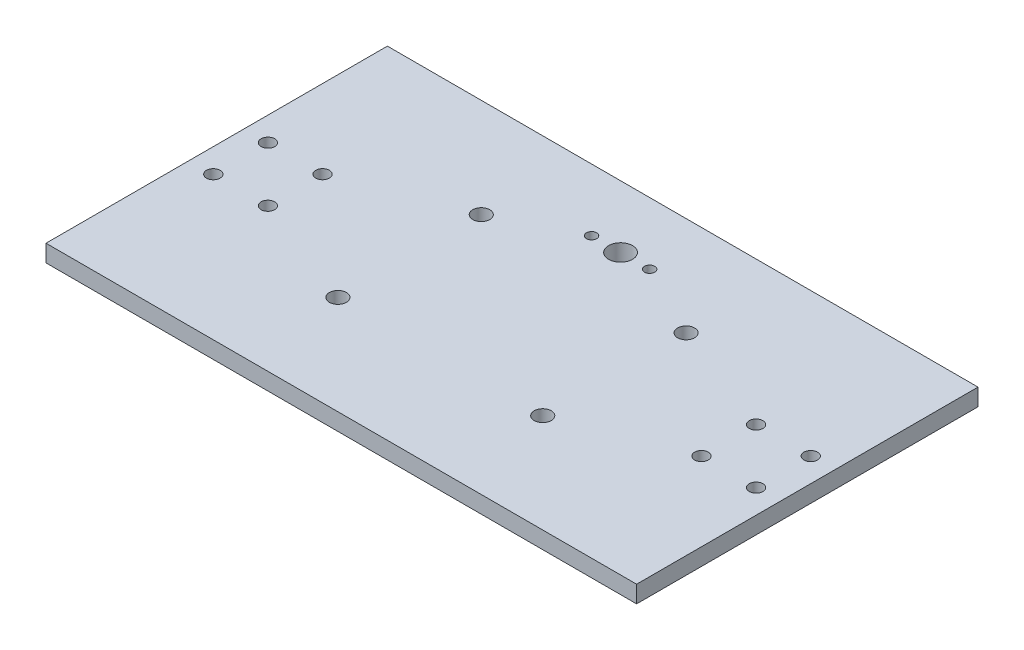
SolidWorks part; units mm, degrees
ref_plane "Front Plane" through (0, 0, 0) normal (0, 0, 1) x (1, 0, 0)
ref_plane "Top Plane" through (0, 0, 0) normal (0, 1, 0) x (1, 0, 0)
ref_plane "Right Plane" through (0, 0, 0) normal (1, 0, 0) x (0, 0, -1)
sketch "Sketch1" plane through (0, 0, 0) normal (0, 1, 0) x (1, 0, 0)
  line L0 (0, 23.9276) -> (0, -82.0412) construction
  line L5 (-36.5, -4.3) -> (-23.5, -4.3) construction
  line L6 (-36.5, -4.3) -> (-36.5, -59.3) construction
  line L7 (-36.5, -59.3) -> (-23.5, -59.3) construction
  line L8 (-23.5, -4.3) -> (-23.5, -59.3) construction
  line L9 (-36.5, -4.3) -> (-23.5, -59.3) construction
  line L10 (-36.5, -59.3) -> (-23.5, -4.3) construction
  line L11 (-30, -31.8) -> (30, -31.8) construction
  line L12 (-30, -27.8) -> (30, -27.8) construction
  line L13 (-30, -29) -> (30, -29) construction
  line L14 (36.5, -59.3) -> (23.5, -4.3) construction
  line L15 (36.5, -4.3) -> (23.5, -59.3) construction
  line L16 (23.5, -4.3) -> (23.5, -59.3) construction
  line L17 (36.5, -59.3) -> (23.5, -59.3) construction
  line L18 (36.5, -4.3) -> (36.5, -59.3) construction
  line L19 (36.5, -4.3) -> (23.5, -4.3) construction
  line L20 (-63.5, -39.8) -> (-79.5, -23.8) construction
  line L21 (-86.5, 18.2) -> (86.5, 18.2)
  line L22 (-86.5, 18.2) -> (-86.5, -81.8)
  line L23 (-86.5, -81.8) -> (86.5, -81.8)
  line L24 (86.5, 18.2) -> (86.5, -81.8)
  line L25 (63.5, -23.8) -> (79.5, -23.8) construction
  line L26 (63.5, -23.8) -> (63.5, -39.8) construction
  line L27 (63.5, -39.8) -> (79.5, -39.8) construction
  line L28 (79.5, -23.8) -> (79.5, -39.8) construction
  line L29 (63.5, -23.8) -> (79.5, -39.8) construction
  line L30 (63.5, -39.8) -> (79.5, -23.8) construction
  line L31 (-63.5, -23.8) -> (-79.5, -39.8) construction
  line L32 (-79.5, -23.8) -> (-79.5, -39.8) construction
  line L33 (-63.5, -39.8) -> (-79.5, -39.8) construction
  line L34 (-63.5, -23.8) -> (-63.5, -39.8) construction
  line L35 (-63.5, -23.8) -> (-79.5, -23.8) construction
  circle A0 centre (0, 0) radius 12.5 construction
  circle A1 centre (0, 0) radius 3.5
  circle A2 centre (0, 0) radius 8.5 construction
  circle A3 centre (-8.5, 0) radius 1.5
  circle A4 centre (8.5, 0) radius 1.5
  circle A5 centre (0, 0) radius 29 construction
  circle A6 centre (-30, -10.8) radius 2.5
  circle A7 centre (-30, -52.8) radius 2.5
  circle A8 centre (30, -52.8) radius 2.5
  circle A9 centre (30, -10.8) radius 2.5
  circle A10 centre (63.5, -23.8) radius 2
  circle A11 centre (79.5, -23.8) radius 2
  circle A12 centre (79.5, -39.8) radius 2
  circle A13 centre (63.5, -39.8) radius 2
  circle A14 centre (-63.5, -39.8) radius 2
  circle A15 centre (-79.5, -39.8) radius 2
  circle A16 centre (-79.5, -23.8) radius 2
  circle A17 centre (-63.5, -23.8) radius 2
  point P8 (-30, -31.8)
  point P12 (0, 0)
  point P25 (0, -31.8)
  point P26 (0, -29.0568)
  point P30 (0, -27.8)
  point P33 (0, -29)
  point P44 (0, -81.8)
  point P45 (71.5, -31.8)
  point P62 (-71.5, -31.8)
  point P63 (0, 0)
  point P64 (0, 0)
  dimension "D1" = 25
  dimension "D2" = 7
  dimension "D3" = 17
  dimension "D4" = 3
  dimension "D9" = 21
  dimension "D6" = 58
  dimension "D11" = 5
  dimension "D15" = 50
  dimension "D19" = 4
  dimension "D7" = 13
  dimension "D8" = 55
  dimension "D10" = 21
  dimension "D12" = 23.5
  dimension "D13" = 4
  dimension "D14" = 1.2
  dimension "D16" = 173
  dimension "D17" = 50
  dimension "D18" = 16
  dimension "D20" = 35
  dimension "D5" = 2
extrude "Boss-Extrude1" add sketch "Sketch1" along normal blind 5
